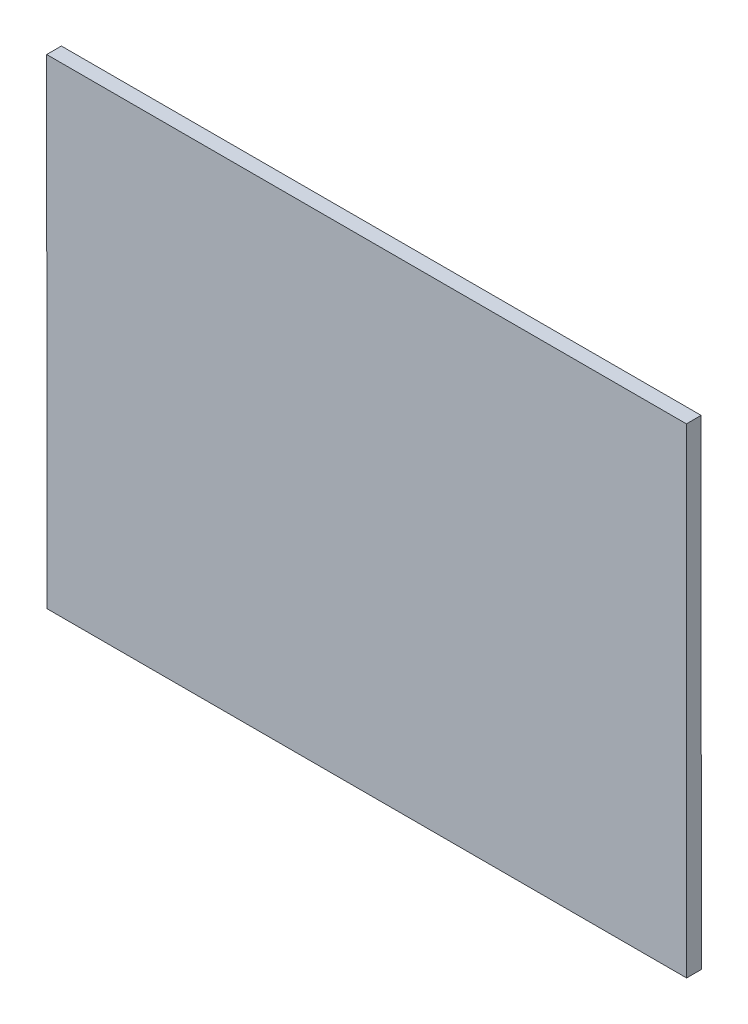
SolidWorks part; units mm, degrees
ref_plane "前视基准面" through (0, 0, 0) normal (0, 0, 1) x (1, 0, 0)
ref_plane "上视基准面" through (0, 0, 0) normal (0, 1, 0) x (1, 0, 0)
ref_plane "右视基准面" through (0, 0, 0) normal (1, 0, 0) x (0, 0, -1)
sketch "草图1" plane through (0, 0, 0) normal (0, 0, 1) x (1, 0, 0)
  line L0 (167.2658, 85.6265) -> (267.2629, 85.6265)
  line L1 (167.23, 160.6265) -> (267.23, 160.6265)
  line L2 (167.23, 160.6265) -> (167.2658, 85.6265)
  line L3 (267.23, 160.6265) -> (267.2629, 85.6265)
  dimension "D1" = 100
  dimension "D2" = 75
extrude "凸台-拉伸1" add sketch "草图1" along normal blind 2.3
